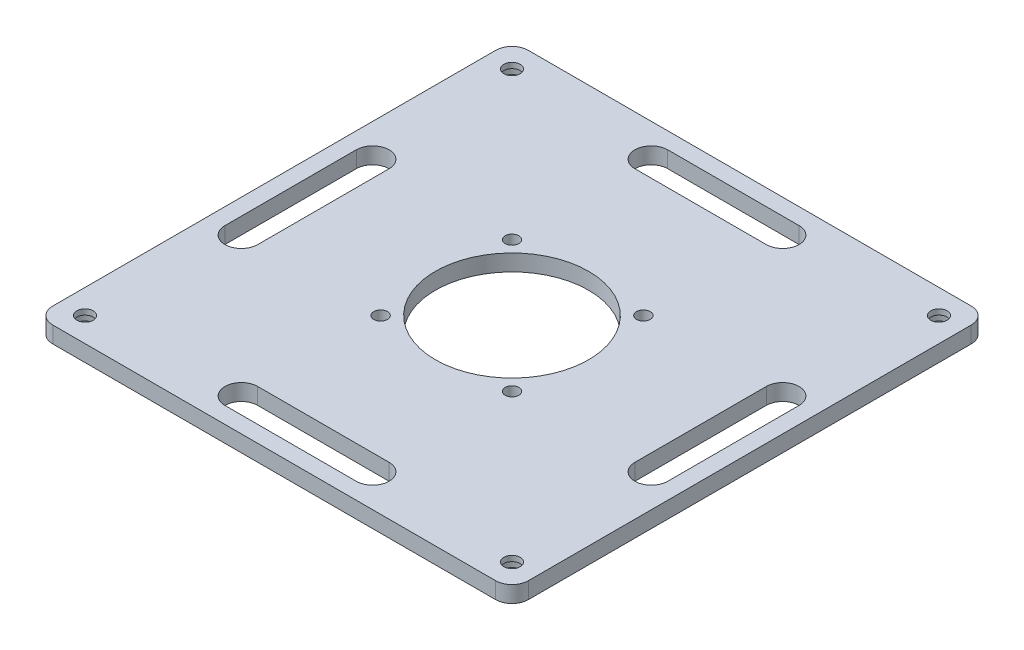
SolidWorks part; units mm, degrees
ref_plane "前基準面" through (0, 0, 0) normal (0, 0, 1) x (1, 0, 0)
ref_plane "上基準面" through (0, 0, 0) normal (0, 1, 0) x (1, 0, 0)
ref_plane "右基準面" through (0, 0, 0) normal (1, 0, 0) x (0, 0, -1)
ref_plane "平面1" through (0, -37, 0) normal (0, 1, 0) x (1, 0, 0)
sketch "草圖1" plane through (0, -37, 0) normal (0, 1, 0) x (1, 0, 0)
  line L0 (-43.45, -43.45) -> (43.45, -43.45)
  line L1 (43.45, -43.45) -> (43.45, 43.45)
  line L2 (43.45, 43.45) -> (-43.45, 43.45)
  line L3 (-43.45, 43.45) -> (-43.45, -43.45)
extrude "填料-伸長1" add sketch "草圖1" against normal blind 3
hole_wizard "M2.5 六角頭機械螺釘的柱孔1" positions "草圖3" profile "草圖2" counterbore size "M2.5" standard "Ansi Metric"
sketch "草圖3" plane through (0, -40, 0) normal (0, -1, 0) x (-1, 0, 0)
  point P0 (39, 39)
  point P1 (-39, 39)
  point P2 (-39, -39)
  point P3 (39, -39)
sketch "草圖2" plane through (-39, -40, -39) normal (1, 0, 0) x (0, 0, -1)
  line L0 (0, 0) -> (0, 3)
  line L1 (0, 3) -> (1.5, 3)
  line L3 (1.5, 3) -> (1.5, 2)
  line L4 (1.5, 2) -> (3, 2)
  line L5 (3, 2) -> (3, 0)
  line L7 (3, 0) -> (0, 0)
  line L11 (0, -6.35) -> (0, 107.95) construction
  dimension "砮 ふ 畖" = 3
  dimension "砮 ふ瞏 " = 3
  dimension "琖ふ 畖" = 6
  dimension "琖ふ瞏 " = 2
hole_wizard "Ø2.0 (2) 直徑孔1" positions "草圖5" profile "草圖4" hole size "Ø2.0" standard "Ansi Metric"
sketch "草圖5" plane through (0, -37, 0) normal (0, 1, 0) x (1, 0, 0)
  point P0 (5, -10)
  point P1 (0, -10)
  point P2 (-5, -10)
  point P3 (-10, -5)
  point P4 (-10, 0)
  point P5 (-10, 5)
  point P6 (-5, 10)
  point P7 (0, 10)
  point P8 (5, 10)
  point P9 (10, 5)
  point P10 (10, 0)
  point P11 (10, -5)
  point P12 (5, -5)
  point P13 (0, -5)
  point P14 (-5, -5)
  point P15 (-5, 0)
  point P16 (-5, 5)
  point P17 (0, 5)
  point P18 (5, 5)
  point P19 (5, 0)
  point P20 (0, 0)
  point P21 (-37.5, 3)
  point P22 (-37.5, 0)
  point P23 (-37.5, -3)
  point P24 (3, 37.5)
  point P25 (0, 37.5)
  point P26 (-3, 37.5)
  point P27 (37.5, -3)
  point P28 (37.5, 0)
  point P29 (37.5, 3)
  point P30 (-3, -37.5)
  point P31 (0, -37.5)
  point P32 (3, -37.5)
sketch "草圖4" plane through (5, -37, 10) normal (1, 0, 0) x (0, 0, 1)
  line L0 (0, 0) -> (0, 3)
  line L1 (0, 3) -> (1, 3)
  line L2 (1, 3) -> (1, 0)
  line L5 (1, 0) -> (0, 0)
  line L11 (0, -6.35) -> (0, 107.95) construction
  dimension "砮 ふ 畖" = 2
  dimension "砮 ふ瞏 " = 3
hole_wizard "Ø2.5 (2.5) 直徑孔1" positions "草圖7" profile "草圖6" hole size "Ø2.5" standard "Ansi Metric"
sketch "草圖7" plane through (0, -40, 0) normal (0, -1, 0) x (-1, 0, 0)
  point P0 (12, 12)
  point P1 (-12, 12)
  point P2 (12, -12)
  point P3 (-12, -12)
sketch "草圖6" plane through (-12, -40, -12) normal (1, 0, 0) x (0, 0, -1)
  line L0 (0, 0) -> (0, 3)
  line L1 (0, 3) -> (1.25, 3)
  line L2 (1.25, 3) -> (1.25, 0)
  line L5 (1.25, 0) -> (0, 0)
  line L11 (0, -6.35) -> (0, 107.95) construction
  dimension "砮 ふ 畖" = 2.5
  dimension "砮 ふ瞏 " = 3
fillet "圓角1" radius 3 4 edges at (-43.45, -38.5, 43.45) (-43.45, -38.5, -43.45) (43.45, -38.5, 43.45) (43.45, -38.5, -43.45)
sketch "草圖8" plane through (0, -37, 0) normal (0, 1, 0) x (1, 0, 0)
  line L0 (-37.45, -12) -> (-37.45, 12) construction
  line L1 (-40.45, -12) -> (-40.45, 12)
  line L2 (-34.45, -12) -> (-34.45, 12)
  line L4 (-43.45, 40.45) -> (-43.45, -40.45) construction
  line L5 (0, 0) -> (-43.45, 0) construction
  line L6 (-12, 37.45) -> (12, 37.45) construction
  line L7 (-12, 40.45) -> (12, 40.45)
  line L8 (-12, 34.45) -> (12, 34.45)
  line L9 (37.45, 12) -> (37.45, -12) construction
  line L10 (40.45, 12) -> (40.45, -12)
  line L11 (34.45, 12) -> (34.45, -12)
  line L12 (12, -37.45) -> (-12, -37.45) construction
  line L13 (12, -40.45) -> (-12, -40.45)
  line L14 (12, -34.45) -> (-12, -34.45)
  circle A0 centre (0, 0) radius 14
  arc A1 (-40.45, -12) -> (-34.45, -12) centre (-37.45, -12) ccw
  arc A2 (-34.45, 12) -> (-40.45, 12) centre (-37.45, 12) ccw
  arc A4 (-12, 40.45) -> (-12, 34.45) centre (-12, 37.45) ccw
  arc A5 (12, 34.45) -> (12, 40.45) centre (12, 37.45) ccw
  arc A6 (40.45, 12) -> (34.45, 12) centre (37.45, 12) ccw
  arc A7 (34.45, -12) -> (40.45, -12) centre (37.45, -12) ccw
  arc A8 (12, -40.45) -> (12, -34.45) centre (12, -37.45) ccw
  arc A9 (-12, -34.45) -> (-12, -40.45) centre (-12, -37.45) ccw
  point P6 (-37.45, 0)
  point P21 (0, 37.45)
  point P28 (37.45, 0)
  point P35 (0, -37.45)
  point P40 (0, 0)
  dimension "D1" = 28
  dimension "D2" = 6
  dimension "D3" = 6
  dimension "D4" = 24
  dimension "D5" = 4
extrude "除料-伸長1" cut sketch "草圖8" against normal through all
